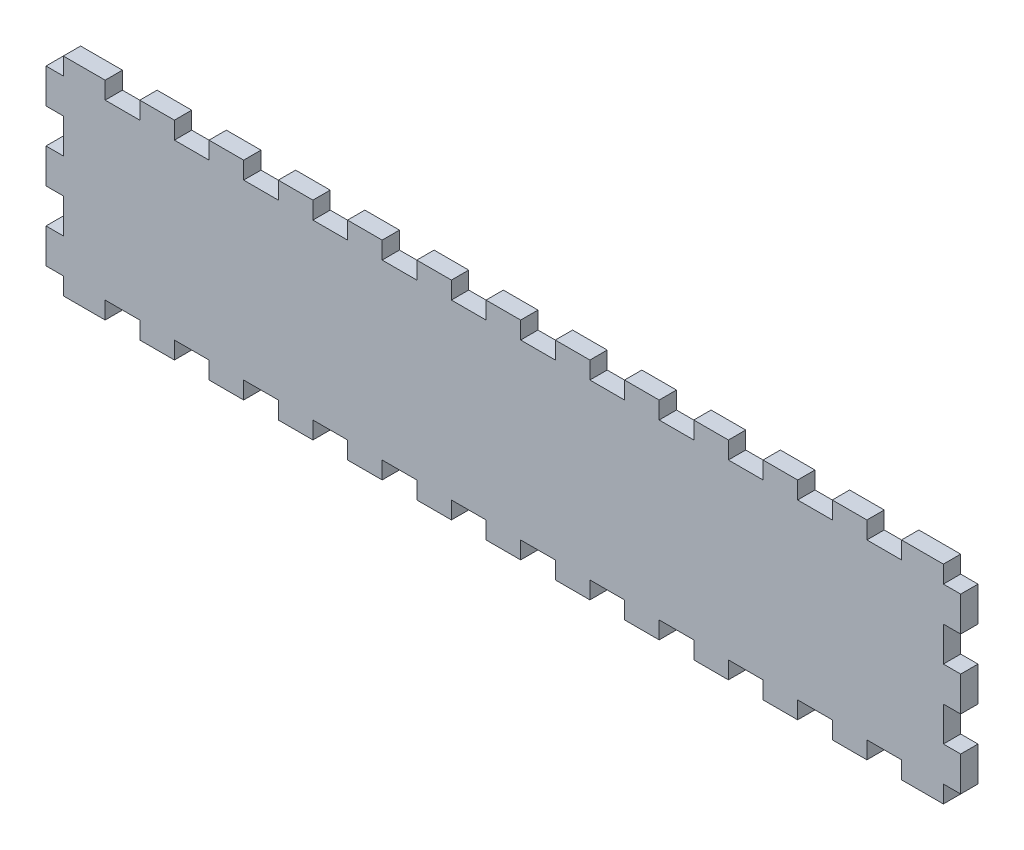
SolidWorks part; units mm, degrees
ref_plane "Front Plane" through (0, 0, 0) normal (0, 0, 1) x (1, 0, 0)
ref_plane "Top Plane" through (0, 0, 0) normal (0, 1, 0) x (1, 0, 0)
ref_plane "Right Plane" through (0, 0, 0) normal (1, 0, 0) x (0, 0, -1)
sketch "Sketch2" plane through (0, 0, -6) normal (0, 0, 1) x (1, 0, 0)
  line L0 (-152.5, 6) -> (-138, 6)
  line L1 (-138, 6) -> (-138, 0)
  line L2 (-138, 0) -> (-126, 0)
  line L3 (-126, 0) -> (-126, 6)
  line L4 (-126, 6) -> (-114, 6)
  line L5 (-114, 6) -> (-114, 0)
  line L6 (-114, 0) -> (-102, 0)
  line L7 (-102, 0) -> (-102, 6)
  line L8 (-102, 6) -> (-90, 6)
  line L9 (-90, 6) -> (-90, 0)
  line L10 (-90, 0) -> (-78, 0)
  line L11 (-78, 0) -> (-78, 6)
  line L12 (-78, 6) -> (-66, 6)
  line L13 (-66, 6) -> (-66, 0)
  line L14 (-66, 0) -> (-54, 0)
  line L15 (-54, 0) -> (-54, 6)
  line L16 (-54, 6) -> (-42, 6)
  line L17 (-42, 6) -> (-42, 0)
  line L18 (-42, 0) -> (-30, 0)
  line L19 (-30, 0) -> (-30, 6)
  line L20 (-30, 6) -> (-18, 6)
  line L21 (-18, 6) -> (-18, 0)
  line L22 (-18, 0) -> (-6, 0)
  line L23 (-6, 0) -> (-6, 6)
  line L24 (-6, 6) -> (6, 6)
  line L25 (6, 6) -> (6, 0)
  line L26 (6, 0) -> (18, 0)
  line L27 (18, 0) -> (18, 6)
  line L28 (18, 6) -> (30, 6)
  line L29 (30, 6) -> (30, 0)
  line L30 (30, 0) -> (42, 0)
  line L31 (42, 0) -> (42, 6)
  line L32 (42, 6) -> (54, 6)
  line L33 (54, 6) -> (54, 0)
  line L34 (54, 0) -> (66, 0)
  line L35 (66, 0) -> (66, 6)
  line L36 (66, 6) -> (78, 6)
  line L37 (78, 6) -> (78, 0)
  line L38 (78, 0) -> (90, 0)
  line L39 (90, 0) -> (90, 6)
  line L40 (90, 6) -> (102, 6)
  line L41 (102, 6) -> (102, 0)
  line L42 (102, 0) -> (114, 0)
  line L43 (114, 0) -> (114, 6)
  line L44 (114, 6) -> (126, 6)
  line L45 (126, 6) -> (126, 0)
  line L46 (126, 0) -> (138, 0)
  line L47 (138, 0) -> (138, 6)
  line L48 (138, 6) -> (152.5, 6)
  line L49 (152.5, 6) -> (152.5, 0)
  line L50 (152.5, 0) -> (158.5, 0)
  line L51 (158.5, 0) -> (158.5, -12)
  line L52 (158.5, -12) -> (152.5, -12)
  line L53 (152.5, -12) -> (152.5, -24)
  line L54 (152.5, -24) -> (158.5, -24)
  line L55 (158.5, -24) -> (158.5, -36)
  line L56 (158.5, -36) -> (152.5, -36)
  line L57 (152.5, -36) -> (152.5, -48)
  line L58 (152.5, -48) -> (158.5, -48)
  line L59 (158.5, -48) -> (158.5, -60)
  line L60 (158.5, -60) -> (152.5, -60)
  line L61 (152.5, -60) -> (152.5, -66)
  line L62 (-152.5, 6) -> (-152.5, 0)
  line L63 (-152.5, 0) -> (-158.5, 0)
  line L64 (-158.5, 0) -> (-158.5, -12)
  line L65 (-158.5, -12) -> (-152.5, -12)
  line L66 (-152.5, -12) -> (-152.5, -24)
  line L67 (-152.5, -24) -> (-158.5, -24)
  line L68 (-158.5, -24) -> (-158.5, -36)
  line L69 (-158.5, -36) -> (-152.5, -36)
  line L70 (-152.5, -36) -> (-152.5, -48)
  line L71 (-152.5, -48) -> (-158.5, -48)
  line L72 (-158.5, -48) -> (-158.5, -60)
  line L73 (-158.5, -60) -> (-152.5, -60)
  line L74 (-152.5, -60) -> (-152.5, -66)
  line L75 (-152.5, -66) -> (152.5, -66)
extrude "Boss-Extrude1" add sketch "Sketch2" along normal blind 6 contours L75 L61 L60 L59 L58 L57 L56 L55 L54 L53 L52 L51 L50 L49 L48 L47 L46 L45 L44 L43 L42 L41 L40 L39 L38 L37 L36 L35 L34 L33 L32 L31 L30 L29 L28 L27 L26 L25 L24 L23 L22 L21 L20 L19 L18 L17 L16 L15 L14 L13 L12 L11 L10 L9 L8 L7 L6 L5 L4 L3 L2 L1 L0 L62 L63 L64 L65 L66 L67 L68 L69 L70 L71 L72 L73 L74
sketch "Sketch3" plane through (0, 0, 0) normal (0, 0, 1) x (1, 0, 0)
  line L0 (-138, -66) -> (-138, -60)
  line L1 (-152.5, -66) -> (152.5, -66) construction
  line L2 (-138, -60) -> (-126, -60)
  line L3 (-126, -60) -> (-126, -66)
  line L4 (-126, -66) -> (-138, -66)
  line L5 (-102, -66) -> (-114, -66)
  line L6 (-114, -66) -> (-114, -60)
  line L7 (-114, -60) -> (-102, -60)
  line L8 (-102, -60) -> (-102, -66)
  line L9 (-78, -66) -> (-90, -66)
  line L10 (-90, -66) -> (-90, -60)
  line L11 (-90, -60) -> (-78, -60)
  line L12 (-78, -60) -> (-78, -66)
  line L13 (-54, -66) -> (-66, -66)
  line L14 (-66, -66) -> (-66, -60)
  line L15 (-66, -60) -> (-54, -60)
  line L16 (-54, -60) -> (-54, -66)
  line L17 (-30, -66) -> (-42, -66)
  line L18 (-42, -66) -> (-42, -60)
  line L19 (-42, -60) -> (-30, -60)
  line L20 (-30, -60) -> (-30, -66)
  line L21 (-6, -66) -> (-18, -66)
  line L22 (-18, -66) -> (-18, -60)
  line L23 (-18, -60) -> (-6, -60)
  line L24 (-6, -60) -> (-6, -66)
  line L25 (18, -66) -> (6, -66)
  line L26 (6, -66) -> (6, -60)
  line L27 (6, -60) -> (18, -60)
  line L28 (18, -60) -> (18, -66)
  line L29 (42, -66) -> (30, -66)
  line L30 (30, -66) -> (30, -60)
  line L31 (30, -60) -> (42, -60)
  line L32 (42, -60) -> (42, -66)
  line L33 (66, -66) -> (54, -66)
  line L34 (54, -66) -> (54, -60)
  line L35 (54, -60) -> (66, -60)
  line L36 (66, -60) -> (66, -66)
  line L37 (90, -66) -> (78, -66)
  line L38 (78, -66) -> (78, -60)
  line L39 (78, -60) -> (90, -60)
  line L40 (90, -60) -> (90, -66)
  line L41 (114, -66) -> (102, -66)
  line L42 (102, -66) -> (102, -60)
  line L43 (102, -60) -> (114, -60)
  line L44 (114, -60) -> (114, -66)
  line L45 (138, -66) -> (126, -66)
  line L46 (126, -66) -> (126, -60)
  line L47 (126, -60) -> (138, -60)
  line L48 (138, -60) -> (138, -66)
  line L49 (-126, -66) -> (-102, -66) construction
  dimension "D1" = 12
  dimension "D2" = 6
  dimension "D4" = 24
  dimension "D3" = 12
extrude "Cut-Extrude1" cut sketch "Sketch3" against normal blind 6
